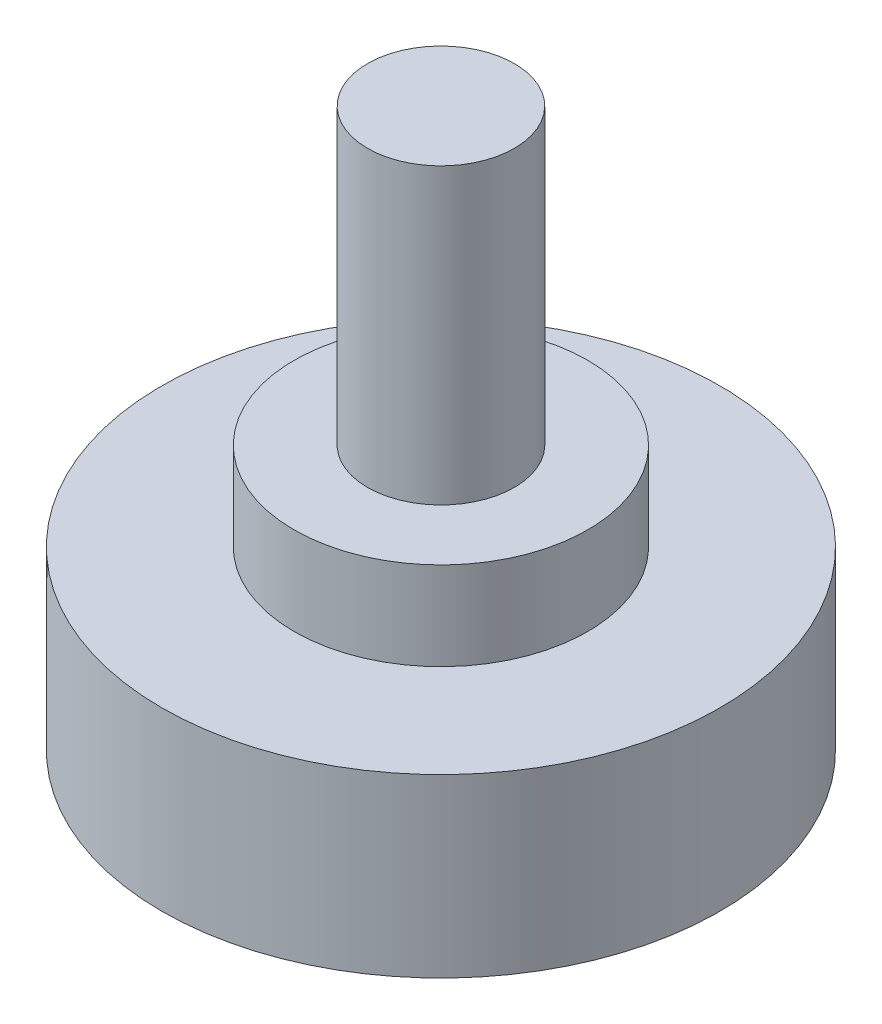
SolidWorks part; units mm, degrees
ref_plane "前视基准面" through (0, 0, 0) normal (0, 0, 1) x (1, 0, 0)
ref_plane "上视基准面" through (0, 0, 0) normal (0, 1, 0) x (1, 0, 0)
ref_plane "右视基准面" through (0, 0, 0) normal (1, 0, 0) x (0, 0, -1)
sketch "草图1" plane through (0, 0, 0) normal (0, 1, 0) x (1, 0, 0)
  circle A0 centre (0, 0) radius 19
  dimension "D1" = 38
extrude "凸台-拉伸1" add sketch "草图1" along normal blind 12
sketch "草图2" plane through (0, 12, 0) normal (0, 1, 0) x (1, 0, 0)
  circle A0 centre (0, 0) radius 10
  dimension "D1" = 20
extrude "凸台-拉伸2" add sketch "草图2" along normal blind 6
sketch "草图3" plane through (0, 18, 0) normal (0, 1, 0) x (1, 0, 0)
  circle A0 centre (0, 0) radius 5
  dimension "D1" = 10
extrude "凸台-拉伸3" add sketch "草图3" along normal blind 20
